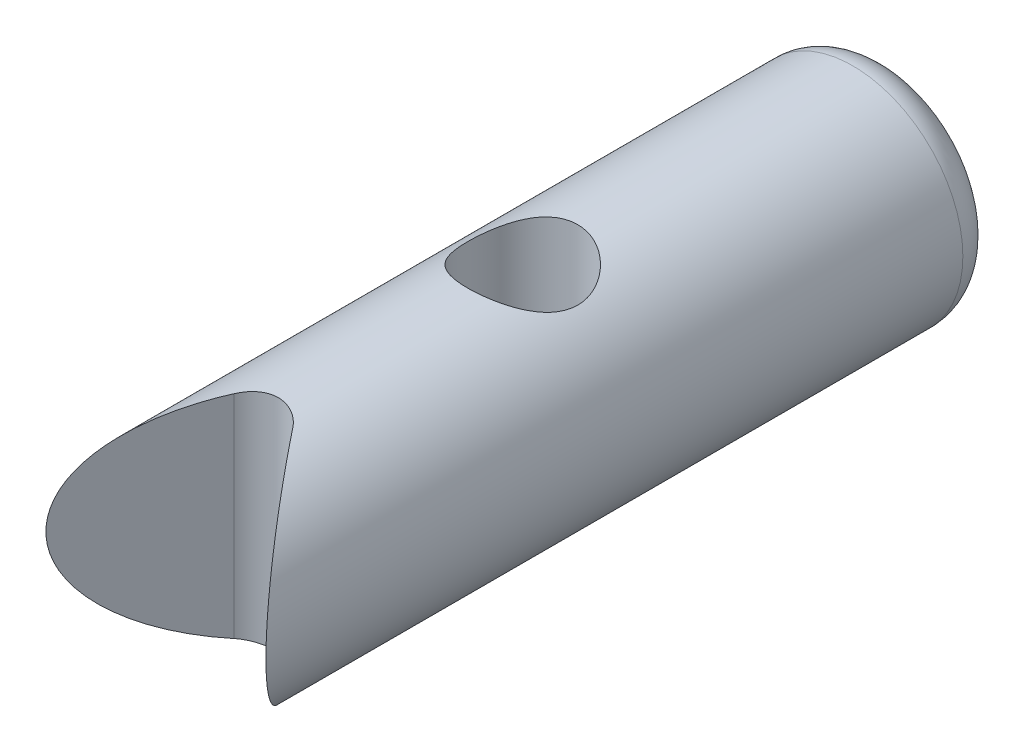
SolidWorks part; units mm, degrees
ref_plane "Alzado" through (0, 0, 0) normal (0, 0, 1) x (1, 0, 0)
ref_plane "Planta" through (0, 0, 0) normal (0, 1, 0) x (1, 0, 0)
ref_plane "Vista lateral" through (0, 0, 0) normal (1, 0, 0) x (0, 0, -1)
sketch "Croquis1" plane through (0, 0, 0) normal (0, 0, 1) x (1, 0, 0)
  circle A0 centre (0, 0) radius 3
extrude "Saliente-Extruir2" add sketch "Croquis1" along normal blind 20 contours A0
sketch "Croquis2" plane through (0, 0, 0) normal (0, 1, 0) x (1, 0, 0)
  line L0 (-3, -20) -> (0, -16)
  line L1 (-3, 0) -> (-3, -20) construction
  line L2 (-3, -20) -> (3, -20) construction
  line L3 (0, -16) -> (3, -20)
  line L4 (3, -20) -> (-3, -20)
  line L5 (3, 0) -> (-3, 0) construction
  circle A0 centre (0, -10) radius 1.5
  dimension "D1" = 4
  dimension "D2" = 10
extrude "Cortar-Extruir1" cut sketch "Croquis2" against normal through all both and the other way through all
fillet "Redondeo7" radius 1 2 edges at (3, 0, 0) (0, 0, 16)
